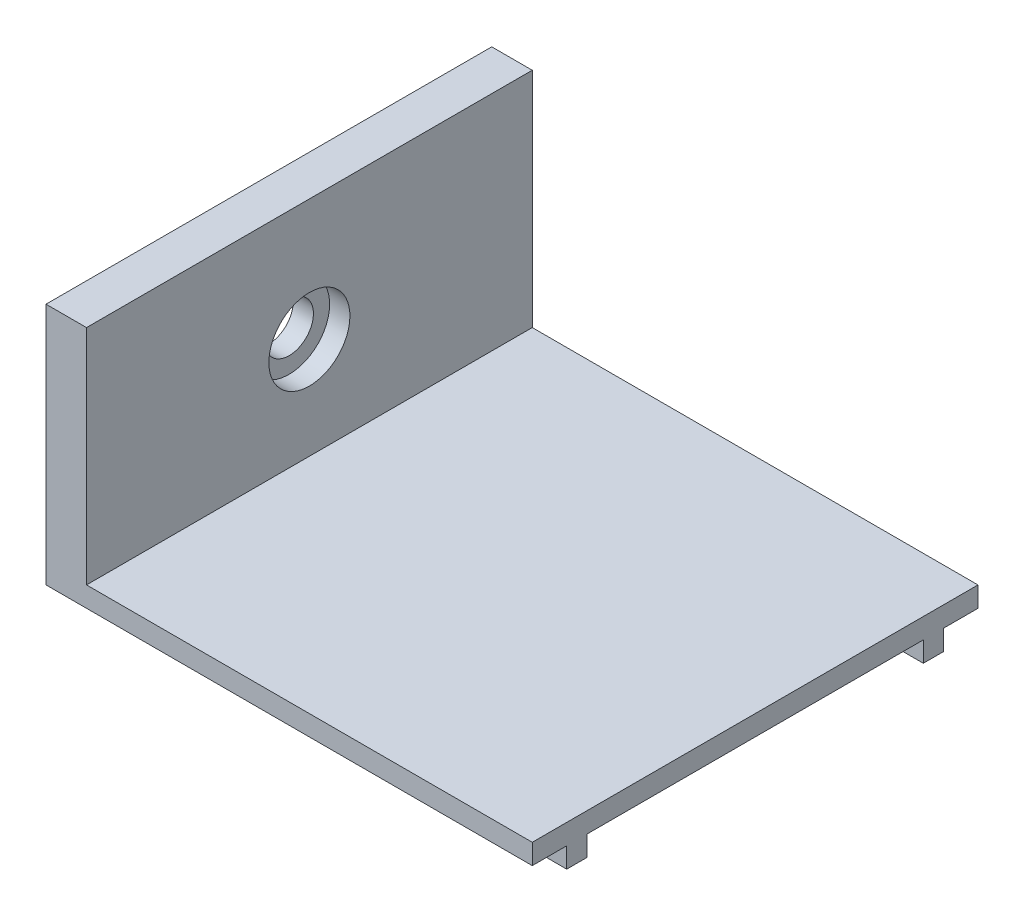
SolidWorks part; units mm, degrees
ref_plane "Front Plane" through (0, 0, 0) normal (0, 0, 1) x (1, 0, 0)
ref_plane "Top Plane" through (0, 0, 0) normal (0, 1, 0) x (1, 0, 0)
ref_plane "Right Plane" through (0, 0, 0) normal (1, 0, 0) x (0, 0, -1)
sketch "Sketch2" plane through (0, 0, 0) normal (0, 0, 1) x (1, 0, 0)
  line L0 (0, 0) -> (0, 60)
  line L5 (0, 60) -> (10, 60)
  line L6 (10, 60) -> (10, 5)
  line L7 (10, 5) -> (120, 5)
  line L8 (120, 5) -> (120, 0)
  line L9 (120, 0) -> (0, 0)
  dimension "D1" = 60
  dimension "D2" = 120
  dimension "D3" = 10
  dimension "D4" = 5
extrude "Boss-Extrude2" add sketch "Sketch2" along normal blind 110
sketch "Sketch3" plane through (0, 0, 0) normal (0, -1, 0) x (1, 0, 0)
  line L0 (0, 110) -> (0, 0) construction
  line L1 (0, 101.5) -> (120, 101.5)
  line L2 (0, 101.5) -> (0, 96.5)
  line L3 (0, 96.5) -> (120, 96.5)
  line L4 (120, 101.5) -> (120, 96.5)
  line L5 (120, 110) -> (120, 0) construction
  line L7 (120, 13.5) -> (0, 13.5)
  line L8 (120, 13.5) -> (120, 8.5)
  line L9 (120, 8.5) -> (0, 8.5)
  line L10 (0, 13.5) -> (0, 8.5)
  line L12 (60, 101.5) -> (60, 110)
  line L13 (0, 110) -> (120, 110) construction
  line L14 (60, 8.5) -> (60, 0)
  line L15 (0, 0) -> (120, 0) construction
  line M12 (120, 0) -> (120, 110)
  line M14 (0, 110) -> (0, 0)
  dimension "D1" = 5
  dimension "D2" = 83
extrude "Boss-Extrude3" add sketch "Sketch3" along normal blind 5 contours L3 L1 M14 M12 | L9 L7 M12 M14
sketch "Sketch4" plane through (0, 0, 0) normal (-1, 0, 0) x (0, 0, 1)
  line L0 (0, 60) -> (0, 0) construction
  line L1 (110, 60) -> (0, 60) construction
  circle A0 centre (55, 30) radius 6
  point P5 (0, 30)
  point P9 (55, 60)
  dimension "D1" = 12
extrude "Cut-Extrude1" cut sketch "Sketch4" against normal blind 5
sketch "Sketch5" plane through (10, 0, 0) normal (1, 0, 0) x (0, 0, -1)
  line L1 (-110, 60) -> (0, 60) construction
  circle A0 centre (-55, 30) radius 10
  point P9 (-55, 60)
  dimension "D1" = 20
  dimension "D2" = 30
extrude "Cut-Extrude2" cut sketch "Sketch5" against normal blind 5
